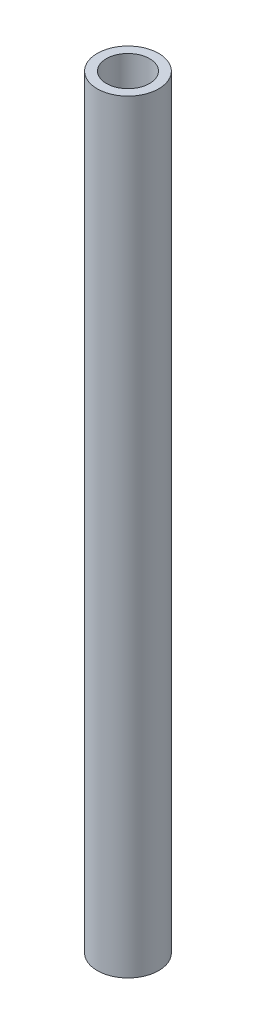
SolidWorks part; units mm, degrees
ref_plane "前视基准面" through (0, 0, 0) normal (0, 0, 1) x (1, 0, 0)
ref_plane "上视基准面" through (0, 0, 0) normal (0, 1, 0) x (1, 0, 0)
ref_plane "右视基准面" through (0, 0, 0) normal (1, 0, 0) x (0, 0, -1)
sketch "草图1" plane through (0, 0, 0) normal (0, 1, 0) x (1, 0, 0)
  circle A0 centre (0, 0) radius 18.5
  circle A1 centre (0, 0) radius 13
  dimension "D1" = 37
  dimension "D2" = 26
extrude "凸台-拉伸1" add sketch "草图1" along normal blind 460
